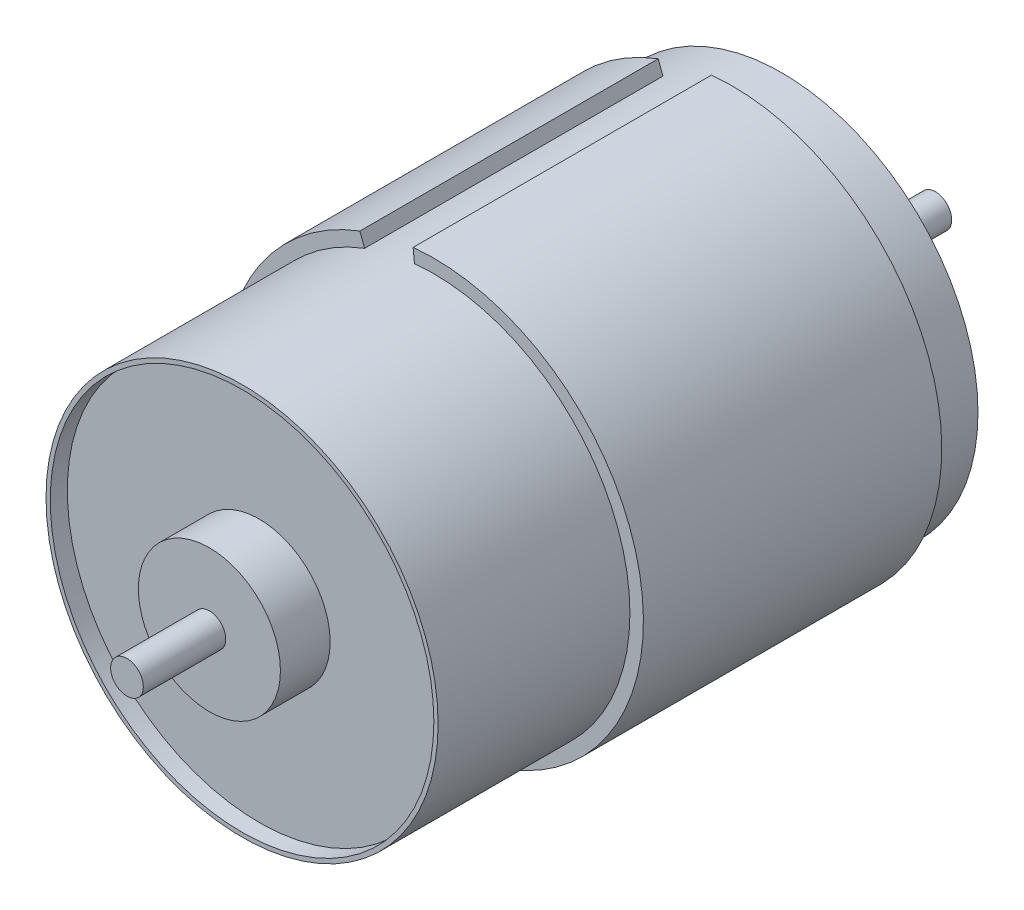
SolidWorks part; units mm, degrees
ref_plane "Front Plane" through (0, 0, 0) normal (0, 0, 1) x (1, 0, 0)
ref_plane "Top Plane" through (0, 0, 0) normal (0, 1, 0) x (1, 0, 0)
ref_plane "Right Plane" through (0, 0, 0) normal (1, 0, 0) x (0, 0, -1)
sketch "Sketch1" plane through (0, 0, 0) normal (0, 0, 1) x (1, 0, 0)
  circle A0 centre (0, 0) radius 13.8
  dimension "D1" = 27.6
extrude "Boss-Extrude1" add sketch "Sketch1" along normal blind 38
sketch "Sketch2" plane through (0, 0, 38) normal (0, 0, 1) x (1, 0, 0)
  line L0 (-1.4588, 14.6777) -> (-1.3648, 13.7323)
  line L2 (-5.2079, 13.8) -> (-4.8725, 12.9112)
  circle A0 centre (0, 0) radius 13.8 construction
  arc A1 (-4.8725, 12.9112) -> (-1.3648, 13.7323) centre (0, 0) ccw
  arc A2 (-5.2079, 13.8) -> (-1.4588, 14.6777) centre (0, 0) ccw
  circle A4 centre (0, 0) radius 13.8 construction
  circle A5 centre (0, 0) radius 14.75 construction
  point P2 (14.75, 0)
  point P8 (13.197, 4.0347)
  dimension "D2" = 15
  dimension "D1" = 0.95
extrude "Boss-Extrude2" add sketch "Sketch2" along normal blind 21 from offset 34.5 offset against normal yes
sketch "Sketch3" plane through (0, 0, 0) normal (0, 0, -1) x (-1, 0, 0)
  circle A0 centre (0, 0) radius 5
  dimension "D1" = 10
extrude "Boss-Extrude3" add sketch "Sketch3" along normal blind 2.8
sketch "Sketch4" plane through (0, 0, 38) normal (0, 0, 1) x (1, 0, 0)
  circle A0 centre (0, 0) radius 13.5
  dimension "D1" = 27
extrude "Cut-Extrude1" cut sketch "Sketch4" against normal blind 1.2
sketch "Sketch5" plane through (0, 0, 36.8) normal (0, 0, 1) x (1, 0, 0)
  circle A0 centre (0, 0) radius 5
  dimension "D1" = 10
extrude "Boss-Extrude4" add sketch "Sketch5" along normal blind 3.5
sketch "Sketch6" plane through (0, 0, 40.3) normal (0, 0, 1) x (1, 0, 0)
  circle A0 centre (0, 0) radius 1.15
  dimension "D1" = 2.3
extrude "Boss-Extrude5" add sketch "Sketch6" along normal blind 5.8
sketch "Sketch7" plane through (0, 0, -2.8) normal (0, 0, -1) x (-1, 0, 0)
  circle A0 centre (0, 0) radius 1.15
  dimension "D1" = 2.3
extrude "Boss-Extrude6" add sketch "Sketch7" along normal blind 8
sketch "Sketch8" plane through (0, 0, 0) normal (0, 0, -1) x (-1, 0, 0)
  line L0 (5.2079, 13.8) -> (1.4588, 14.6777) construction
  line L1 (1.4588, 14.6777) -> (3.3333, 14.2388) construction
  line L2 (3.3333, 14.2388) -> (0, 0) construction
  line L3 (0, 0) -> (-7.7894, 1.8235) construction
  circle A1 centre (-7.7894, 1.8235) radius 1.25
  circle A2 centre (7.7894, -1.8235) radius 1.25
  dimension "D1" = 2.5
  dimension "D2" = 8
extrude "Cut-Extrude2" cut sketch "Sketch8" against normal blind 8
